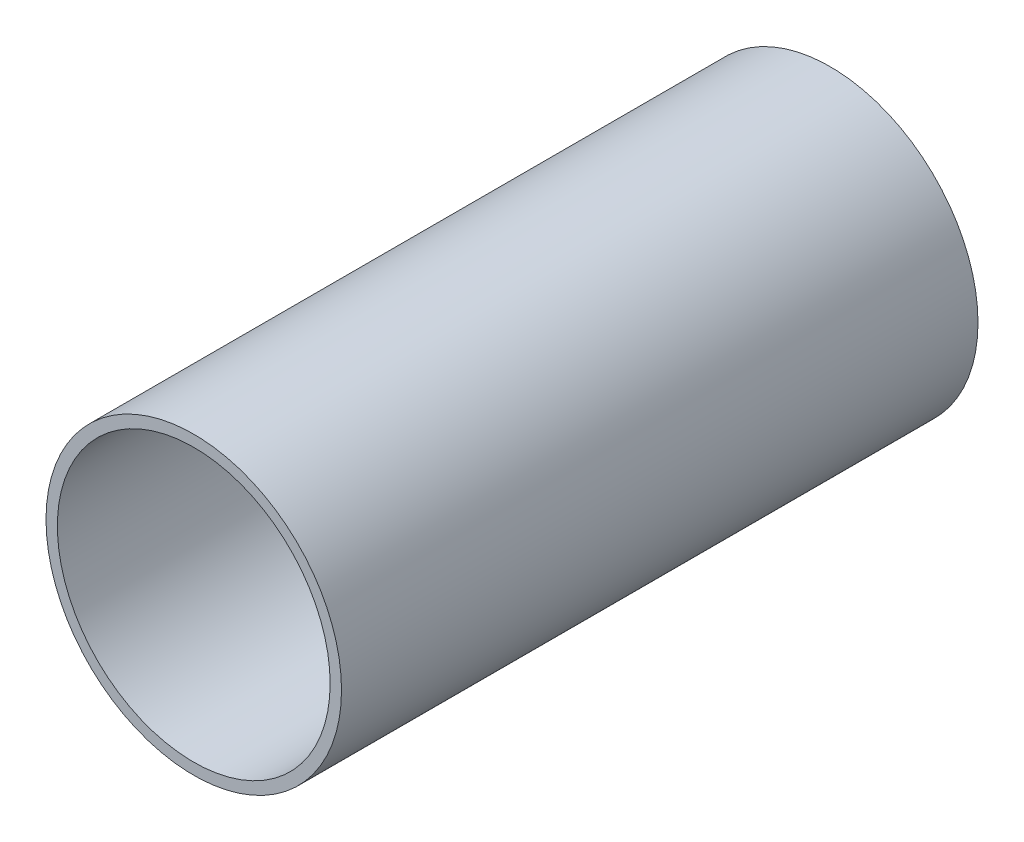
SolidWorks part; units mm, degrees
material "6061 Alloy"
ref_plane "Front Plane" through (0, 0, 0) normal (0, 0, 1) x (1, 0, 0)
ref_plane "Top Plane" through (0, 0, 0) normal (0, 1, 0) x (1, 0, 0)
ref_plane "Right Plane" through (0, 0, 0) normal (1, 0, 0) x (0, 0, -1)
sketch "Sketch1" plane through (0, 0, 0) normal (0, 0, 1) x (1, 0, 0)
  line L1 (27.94, 21.463) -> (-27.94, 21.463) construction
  line L2 (27.94, 21.463) -> (27.94, -21.463) construction
  line L3 (27.94, -21.463) -> (-27.94, -21.463) construction
  line L4 (-27.94, 21.463) -> (-27.94, -21.463) construction
  line L5 (27.94, 21.463) -> (-27.94, -21.463) construction
  line L6 (27.94, -21.463) -> (-27.94, 21.463) construction
  circle A0 centre (0, 0) radius 38.1
  circle A1 centre (0, 0) radius 41.275
  point P0 (0, 0)
  dimension "D3" = 76.2
  dimension "D1" = 42.926
  dimension "D2" = 55.88
  dimension "D4" = 3.175
extrude "Boss-Extrude1" add sketch "Sketch1" along normal blind 177.8
